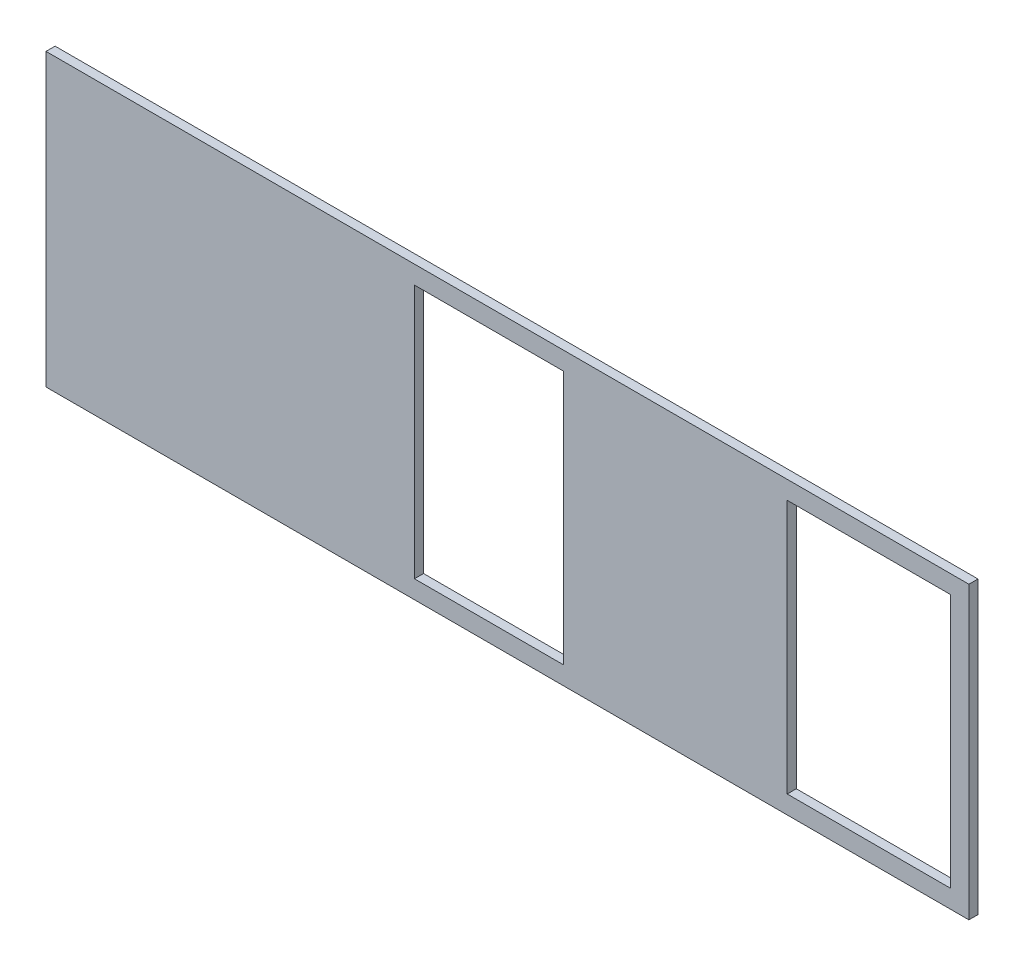
SolidWorks part; units mm, degrees
ref_plane "Front Plane" through (0, 0, 0) normal (0, 0, 1) x (1, 0, 0)
ref_plane "Top Plane" through (0, 0, 0) normal (0, 1, 0) x (1, 0, 0)
ref_plane "Right Plane" through (0, 0, 0) normal (1, 0, 0) x (0, 0, -1)
sketch "Sketch1" plane through (0, 0, 0) normal (0, 0, 1) x (1, 0, 0)
  line L1 (0, 0) -> (322.58, 0)
  line L2 (0, 0) -> (0, 101.6)
  line L3 (0, 101.6) -> (322.58, 101.6)
  line L4 (322.58, 0) -> (322.58, 101.6)
  dimension "D1" = 322.58
  dimension "D2" = 101.6
extrude "Boss-Extrude1" add sketch "Sketch1" along normal blind 3.175
sketch "Sketch2" plane through (0, 0, 3.175) normal (0, 0, 1) x (1, 0, 0)
  line L0 (122.428, 101.6) -> (122.428, 0) construction
  line L1 (322.58, 101.6) -> (0, 101.6) construction
  line L2 (0, 0) -> (322.58, 0) construction
  line L3 (0, 101.6) -> (0, 0) construction
  line L4 (187.198, 101.6) -> (187.198, 0) construction
  line L5 (252.73, 101.6) -> (252.73, 0) construction
  dimension "D1" = 122.428
  dimension "D2" = 64.77
  dimension "D3" = 65.532
sketch "Sketch4" plane through (0, 0, 3.175) normal (0, 0, 1) x (1, 0, 0)
  line L0 (128.778, 95.25) -> (128.778, 6.35)
  line L1 (128.778, 6.35) -> (180.848, 6.35)
  line L2 (180.848, 6.35) -> (180.848, 95.25)
  line L3 (180.848, 95.25) -> (128.778, 95.25)
  line L4 (322.58, 101.6) -> (0, 101.6) construction
  line L5 (0, 0) -> (322.58, 0) construction
  line L6 (187.198, 101.6) -> (187.198, 0) construction
  line L7 (122.428, 101.6) -> (122.428, 0) construction
  line L8 (322.58, 0) -> (322.58, 101.6) construction
  line L9 (259.08, 95.25) -> (316.23, 95.25)
  line L10 (259.08, 95.25) -> (259.08, 6.35)
  line L11 (259.08, 6.35) -> (316.23, 6.35)
  line L12 (316.23, 95.25) -> (316.23, 6.35)
  line L13 (252.73, 101.6) -> (252.73, 0) construction
  point P16 (316.23, 50.8)
  dimension "D1" = 6.35
  dimension "D2" = 6.35
  dimension "D3" = 6.35
  dimension "D4" = 6.35
  dimension "D5" = 6.35
  dimension "D6" = 6.35
  dimension "D7" = 6.35
  dimension "D8" = 6.35
extrude "Cut-Extrude1" cut sketch "Sketch4" against normal through all
